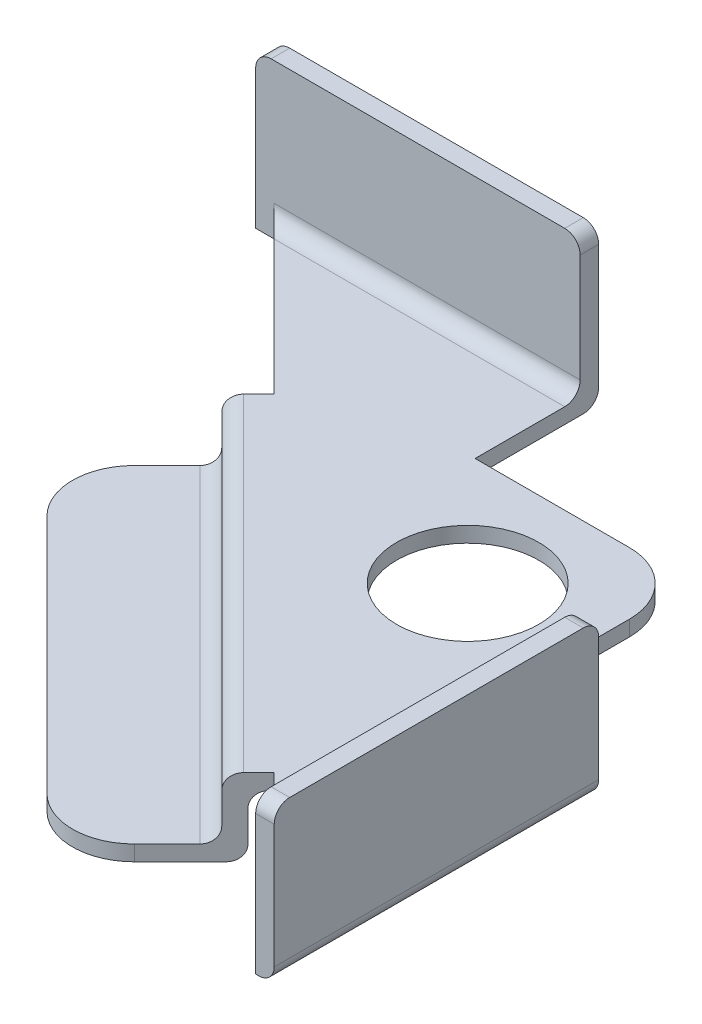
SolidWorks part; units mm, degrees
ref_plane "Front Plane" through (0, 0, 0) normal (0, 0, 1) x (1, 0, 0)
ref_plane "Top Plane" through (0, 0, 0) normal (0, 1, 0) x (1, 0, 0)
ref_plane "Right Plane" through (0, 0, 0) normal (1, 0, 0) x (0, 0, -1)
sketch "Sketch1" plane through (0, 0, 0) normal (0, 1, 0) x (1, 0, 0)
  line L1 (0, 0) -> (21.5, 0)
  line L2 (0, 0) -> (0, 21.5)
  line L3 (0, 21.5) -> (21.5, 21.5)
  line L4 (21.5, 0) -> (21.5, 21.5)
  dimension "D1" = 21.5
  dimension "D2" = 21.5
extrude "Boss-Extrude1" add sketch "Sketch1" along normal blind 0.5
sketch "Sketch2" plane through (0, 0.5, 0) normal (0, 1, 0) x (1, 0, 0)
  line L0 (0, 21.5) -> (21.5, 0)
  line L1 (21.5, 21.5) -> (17.5, 21.5)
  line L2 (21.5, 21.5) -> (21.5, 10.5)
  line L3 (21.5, 10.5) -> (17.5, 10.5)
  line L4 (17.5, 21.5) -> (17.5, 10.5)
  line L5 (21.5, 21.5) -> (10.5, 21.5)
  line L6 (21.5, 21.5) -> (21.5, 17.5)
  line L7 (21.5, 17.5) -> (10.5, 17.5)
  line L8 (10.5, 21.5) -> (10.5, 17.5)
  line L9 (21.5, 0) -> (0, 0)
  line L10 (0, 0) -> (0, 21.5)
  circle A0 centre (13.88, 13.88) radius 2.3
  line M7 (0, 21.5) -> (0, 0)
  line M8 (0, 0) -> (21.5, 0)
  line M9 (21.5, 0) -> (21.5, 21.5)
  line M10 (21.5, 21.5) -> (0, 21.5)
  dimension "D5" = 3.62
  dimension "D1" = 4
  dimension "D2" = 11
  dimension "D3" = 4
  dimension "D4" = 11
  dimension "D6" = 3.62
extrude "Cut-Extrude1" cut sketch "Sketch2" against normal through all contours L0 M7 M8 | A0 | L7 L2 L4 M10 | L7 L4 L3 M9 | L8 L7 L4 M10
fillet "Fillet1" radius 2 1 edges at (17.5, 0.25, -17.5)
sketch "Sketch3" plane through (0, 0.5, 0) normal (0, 1, 0) x (1, 0, 0)
  line L1 (21.5, 10.5) -> (20.9, 10.5)
  line L2 (21.5, 10.5) -> (21.5, 0)
  line L3 (21.5, 0) -> (20.9, 0)
  line L4 (20.9, 10.5) -> (20.9, 0)
  line L5 (10.5, 21.5) -> (0, 21.5)
  line L6 (10.5, 21.5) -> (10.5, 20.9)
  line L7 (10.5, 20.9) -> (0, 20.9)
  line L8 (0, 21.5) -> (0, 20.9)
  dimension "D1" = 0.6
  dimension "D2" = 0.6
extrude "Boss-Extrude2" add sketch "Sketch3" along normal blind 4.5 and the other way blind 0.5
fillet "Fillet11" radius 0.5 8 edges at (5.55, 0.5, -20.9) (0, 5, -21.2) (21.2, 5, 0) (21.2, 5, -10.5) (10.5, 5, -21.2) (5.25, 0, -21.5) (21.5, 0, -5.25) (20.9, 0.5, -5.55)
sketch "Sketch6" plane through (10.75, 0, -10.75) normal (-0.7071, 0, 0.7071) x (0.7071, 0, 0.7071)
  line L0 (-13.6472, 0.5) -> (13.6472, 0.5) construction
  line L1 (-7.5, 0.5) -> (7.5, 0.5)
  line L2 (-7.5, 0.5) -> (-7.5, 0)
  line L3 (-7.5, 0) -> (7.5, 0)
  line L4 (7.5, 0.5) -> (7.5, 0)
  line L5 (-14.3543, 0) -> (14.3543, 0) construction
  dimension "D1" = 15
  dimension "D2" = 7.5
extrude "Boss-Extrude3" add sketch "Sketch6" along normal blind 1.2
sketch "Sketch8" plane through (0, 0, 0) normal (0, -1, 0) x (1, 0, 0)
  line L0 (4.5982, -15.2048) -> (15.2048, -4.5982)
  line L1 (15.2048, -4.5982) -> (15.629, -5.0224)
  line L2 (15.2048, -4.5982) -> (16.0533, -5.4467) construction
  line L3 (15.629, -5.0224) -> (5.0224, -15.629)
  line L4 (4.5982, -15.2048) -> (5.4467, -16.0533) construction
  line L5 (5.0224, -15.629) -> (4.5982, -15.2048)
extrude "Boss-Extrude4" add sketch "Sketch8" along normal blind 2
sketch "Sketch9" plane through (9.9015, 0, -9.9015) normal (-0.7071, 0, 0.7071) x (0.7071, 0, 0.7071)
  line L0 (7.5, -2) -> (7.5, 0.5) construction
  line L1 (-7.5, -2) -> (7.5, -2)
  line L2 (-7.5, -2) -> (-7.5, -1.5)
  line L3 (-7.5, -1.5) -> (7.5, -1.5)
  line L4 (7.5, -2) -> (7.5, -1.5)
  dimension "D1" = 0.5
extrude "Boss-Extrude5" add sketch "Sketch9" along normal blind 4
fillet "Fillet12" radius 0.5 4 edges at (10.3257, 0, -10.3257) (10.3257, -2, -10.3257) (9.9015, 0.5, -9.9015) (9.9015, -1.5, -9.9015)
fillet "Fillet13" radius 2 2 edges at (12.3763, -1.75, -1.7697) (1.7697, -1.75, -12.3763)
